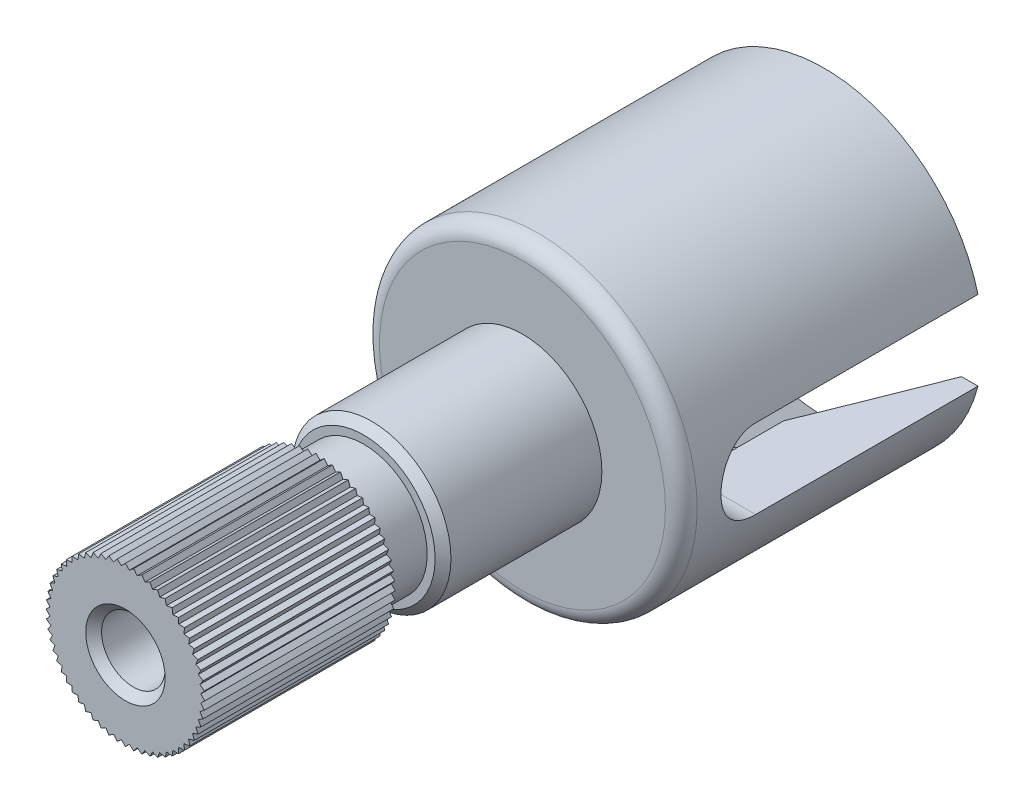
SolidWorks part; units mm, degrees
ref_plane "Plane1" through (0, 0, 0) normal (0, 0, 1) x (1, 0, 0)
ref_plane "Plane2" through (0, 0, 0) normal (0, 1, 0) x (1, 0, 0)
ref_plane "Plane3" through (0, 0, 0) normal (1, 0, 0) x (0, 0, -1)
sketch "Esquisse1" plane through (0, 0, 0) normal (0, 0, 1) x (1, 0, 0)
  circle A0 centre (0, 0) radius 5
  dimension "D1" = 10
extrude "Base-Extrusion" add sketch "Esquisse1" along normal blind 9.5
sketch "Esquisse2" plane through (0, 0, 9.5) normal (0, 0, 1) x (1, 0, 0)
  circle A0 centre (0, 0) radius 2.5
  dimension "D1" = 5
extrude "Boss.-Extru.1" add sketch "Esquisse2" along normal blind 5
fillet "Congé1" radius 0.5
sketch "Esquisse7" plane through (0, 0, 0) normal (1, 0, 0) x (0, 0, -1)
  line L0 (0, 0) -> (-11.8343, 0) construction
  line L1 (-9, 0) -> (0, 0) construction
  line L2 (1, 1.25) -> (-7, 1.25)
  line L3 (1, -1.25) -> (-7, -1.25)
  line L4 (-7, 1.25) -> (-7, -1.25) construction
  line L5 (0, -5) -> (0, 5) construction
  line L6 (1, 1.25) -> (1, -1.25)
  arc A0 (-7, 1.25) -> (-7, -1.25) centre (-7, 0) ccw
  dimension "D1" = 7
  dimension "D2" = 2.5
extrude "Enlèv. mat.-Extru.1" cut sketch "Esquisse7" against normal mid plane 32
sketch "Esquisse8" plane through (0, 0, 0) normal (1, 0, 0) x (0, 0, -1)
  line L0 (0, 4.5) -> (-4, 3)
  line L1 (0, 1.25) -> (0, 5) construction
  line L2 (-4, 3) -> (-8, 3)
  line L3 (-8, 3) -> (-9.5, 0)
  line L4 (-9, 0) -> (0, 0) construction
  line L5 (-9.5, 0) -> (0, 0)
  line L6 (0, 0) -> (0, 4.5)
  line L7 (0, 0) -> (-14.7422, 0) construction
  dimension "D1" = 4
  dimension "D2" = 3
  dimension "D3" = 4
  dimension "D4" = 1.5
  dimension "D5" = 4.5
revolve "Enlèvement de matière-Révolution1" cut sketch "Esquisse8" angle 360 about L7
sketch "Esquisse10" plane through (0, 0, 0) normal (0, 0, 1) x (1, 0, 0)
  line L0 (2.3717, -0.1243) -> (2.4863, -0.2613)
  line L1 (2.3717, -0.1243) -> (2.5, 0)
  line L2 (2.3458, -0.3715) -> (2.4454, -0.5198)
  line L3 (2.3717, 0.1243) -> (2.4863, 0.2613)
  line L4 (2.3717, 0.1243) -> (2.5, 0)
  line L5 (2.3458, -0.3715) -> (2.4863, -0.2613)
  line L6 (2.2941, -0.6147) -> (2.3776, -0.7725)
  line L7 (2.2941, -0.6147) -> (2.4454, -0.5198)
  line L8 (2.2173, -0.8511) -> (2.2839, -1.0168)
  line L9 (2.2173, -0.8511) -> (2.3776, -0.7725)
  line L10 (2.1161, -1.0782) -> (2.1651, -1.25)
  line L11 (2.1161, -1.0782) -> (2.2839, -1.0168)
  line L12 (1.9918, -1.2935) -> (2.0225, -1.4695)
  line L13 (1.9918, -1.2935) -> (2.1651, -1.25)
  line L14 (1.8457, -1.4946) -> (1.8579, -1.6728)
  line L15 (1.8457, -1.4946) -> (2.0225, -1.4695)
  line L16 (1.6794, -1.6794) -> (1.6728, -1.8579)
  line L17 (1.6794, -1.6794) -> (1.8579, -1.6728)
  line L18 (1.4946, -1.8457) -> (1.4695, -2.0225)
  line L19 (1.4946, -1.8457) -> (1.6728, -1.8579)
  line L20 (1.2935, -1.9918) -> (1.25, -2.1651)
  line L21 (1.2935, -1.9918) -> (1.4695, -2.0225)
  line L22 (1.0782, -2.1161) -> (1.0168, -2.2839)
  line L23 (1.0782, -2.1161) -> (1.25, -2.1651)
  line L24 (0.8511, -2.2173) -> (0.7725, -2.3776)
  line L25 (0.8511, -2.2173) -> (1.0168, -2.2839)
  line L26 (0.6147, -2.2941) -> (0.5198, -2.4454)
  line L27 (0.6147, -2.2941) -> (0.7725, -2.3776)
  line L28 (0.3715, -2.3458) -> (0.2613, -2.4863)
  line L29 (0.3715, -2.3458) -> (0.5198, -2.4454)
  line L30 (0.1243, -2.3717) -> (0, -2.5)
  line L31 (0.1243, -2.3717) -> (0.2613, -2.4863)
  line L32 (-0.1243, -2.3717) -> (-0.2613, -2.4863)
  line L33 (-0.1243, -2.3717) -> (0, -2.5)
  line L34 (-0.3715, -2.3458) -> (-0.5198, -2.4454)
  line L35 (-0.3715, -2.3458) -> (-0.2613, -2.4863)
  line L36 (-0.6147, -2.2941) -> (-0.7725, -2.3776)
  line L37 (-0.6147, -2.2941) -> (-0.5198, -2.4454)
  line L38 (-0.8511, -2.2173) -> (-1.0168, -2.2839)
  line L39 (-0.8511, -2.2173) -> (-0.7725, -2.3776)
  line L40 (-1.0782, -2.1161) -> (-1.25, -2.1651)
  line L41 (-1.0782, -2.1161) -> (-1.0168, -2.2839)
  line L42 (-1.2935, -1.9918) -> (-1.4695, -2.0225)
  line L43 (-1.2935, -1.9918) -> (-1.25, -2.1651)
  line L44 (-1.4946, -1.8457) -> (-1.6728, -1.8579)
  line L45 (-1.4946, -1.8457) -> (-1.4695, -2.0225)
  line L46 (-1.6794, -1.6794) -> (-1.8579, -1.6728)
  line L47 (-1.6794, -1.6794) -> (-1.6728, -1.8579)
  line L48 (-1.8457, -1.4946) -> (-2.0225, -1.4695)
  line L49 (-1.8457, -1.4946) -> (-1.8579, -1.6728)
  line L50 (-1.9918, -1.2935) -> (-2.1651, -1.25)
  line L51 (-1.9918, -1.2935) -> (-2.0225, -1.4695)
  line L52 (-2.1161, -1.0782) -> (-2.2839, -1.0168)
  line L53 (-2.1161, -1.0782) -> (-2.1651, -1.25)
  line L54 (-2.2173, -0.8511) -> (-2.3776, -0.7725)
  line L55 (-2.2173, -0.8511) -> (-2.2839, -1.0168)
  line L56 (-2.2941, -0.6147) -> (-2.4454, -0.5198)
  line L57 (-2.2941, -0.6147) -> (-2.3776, -0.7725)
  line L58 (-2.3458, -0.3715) -> (-2.4863, -0.2613)
  line L59 (-2.3458, -0.3715) -> (-2.4454, -0.5198)
  line L60 (-2.3717, -0.1243) -> (-2.5, 0)
  line L61 (-2.3717, -0.1243) -> (-2.4863, -0.2613)
  line L62 (-2.3717, 0.1243) -> (-2.4863, 0.2613)
  line L63 (-2.3717, 0.1243) -> (-2.5, 0)
  line L64 (-2.3458, 0.3715) -> (-2.4454, 0.5198)
  line L65 (-2.3458, 0.3715) -> (-2.4863, 0.2613)
  line L66 (-2.2941, 0.6147) -> (-2.3776, 0.7725)
  line L67 (-2.2941, 0.6147) -> (-2.4454, 0.5198)
  line L68 (-2.2173, 0.8511) -> (-2.2839, 1.0168)
  line L69 (-2.2173, 0.8511) -> (-2.3776, 0.7725)
  line L70 (-2.1161, 1.0782) -> (-2.1651, 1.25)
  line L71 (-2.1161, 1.0782) -> (-2.2839, 1.0168)
  line L72 (-1.9918, 1.2935) -> (-2.0225, 1.4695)
  line L73 (-1.9918, 1.2935) -> (-2.1651, 1.25)
  line L74 (-1.8457, 1.4946) -> (-1.8579, 1.6728)
  line L75 (-1.8457, 1.4946) -> (-2.0225, 1.4695)
  line L76 (-1.6794, 1.6794) -> (-1.6728, 1.8579)
  line L77 (-1.6794, 1.6794) -> (-1.8579, 1.6728)
  line L78 (-1.4946, 1.8457) -> (-1.4695, 2.0225)
  line L79 (-1.4946, 1.8457) -> (-1.6728, 1.8579)
  line L80 (-1.2935, 1.9918) -> (-1.25, 2.1651)
  line L81 (-1.2935, 1.9918) -> (-1.4695, 2.0225)
  line L82 (-1.0782, 2.1161) -> (-1.0168, 2.2839)
  line L83 (-1.0782, 2.1161) -> (-1.25, 2.1651)
  line L84 (-0.8511, 2.2173) -> (-0.7725, 2.3776)
  line L85 (-0.8511, 2.2173) -> (-1.0168, 2.2839)
  line L86 (-0.6147, 2.2941) -> (-0.5198, 2.4454)
  line L87 (-0.6147, 2.2941) -> (-0.7725, 2.3776)
  line L88 (-0.3715, 2.3458) -> (-0.2613, 2.4863)
  line L89 (-0.3715, 2.3458) -> (-0.5198, 2.4454)
  line L90 (-0.1243, 2.3717) -> (0, 2.5)
  line L91 (-0.1243, 2.3717) -> (-0.2613, 2.4863)
  line L92 (0.1243, 2.3717) -> (0.2613, 2.4863)
  line L93 (0.1243, 2.3717) -> (0, 2.5)
  line L94 (0.3715, 2.3458) -> (0.5198, 2.4454)
  line L95 (0.3715, 2.3458) -> (0.2613, 2.4863)
  line L96 (0.6147, 2.2941) -> (0.7725, 2.3776)
  line L97 (0.6147, 2.2941) -> (0.5198, 2.4454)
  line L98 (0.8511, 2.2173) -> (1.0168, 2.2839)
  line L99 (0.8511, 2.2173) -> (0.7725, 2.3776)
  line L100 (1.0782, 2.1161) -> (1.25, 2.1651)
  line L101 (1.0782, 2.1161) -> (1.0168, 2.2839)
  line L102 (1.2935, 1.9918) -> (1.4695, 2.0225)
  line L103 (1.2935, 1.9918) -> (1.25, 2.1651)
  line L104 (1.4946, 1.8457) -> (1.6728, 1.8579)
  line L105 (1.4946, 1.8457) -> (1.4695, 2.0225)
  line L106 (1.6794, 1.6794) -> (1.8579, 1.6728)
  line L107 (1.6794, 1.6794) -> (1.6728, 1.8579)
  line L108 (1.8457, 1.4946) -> (2.0225, 1.4695)
  line L109 (1.8457, 1.4946) -> (1.8579, 1.6728)
  line L110 (1.9918, 1.2935) -> (2.1651, 1.25)
  line L111 (1.9918, 1.2935) -> (2.0225, 1.4695)
  line L112 (2.1161, 1.0782) -> (2.2839, 1.0168)
  line L113 (2.1161, 1.0782) -> (2.1651, 1.25)
  line L114 (2.2173, 0.8511) -> (2.3776, 0.7725)
  line L115 (2.2173, 0.8511) -> (2.2839, 1.0168)
  line L116 (2.2941, 0.6147) -> (2.4454, 0.5198)
  line L117 (2.2941, 0.6147) -> (2.3776, 0.7725)
  line L118 (2.3458, 0.3715) -> (2.4863, 0.2613)
  line L119 (2.3458, 0.3715) -> (2.4454, 0.5198)
sketch "Esquisse11" plane through (0, 0, 14.5) normal (0, 0, 1) x (1, 0, 0)
  circle A0 centre (0, 0) radius 2
  dimension "D1" = 4
extrude "Boss.-Extru.2" add sketch "Esquisse11" along normal blind 1.5
sketch "Esquisse12" plane through (0, 0, 16) normal (0, 0, 1) x (1, 0, 0)
  line L0 (-0.1243, 2.3717) -> (0, 2.5)
  line L1 (0, 2.5) -> (0.1243, 2.3717)
  line L2 (0.2613, 2.4863) -> (0.3715, 2.3458)
  line L3 (0.1243, 2.3717) -> (0.2613, 2.4863)
  line L4 (0.5198, 2.4454) -> (0.6147, 2.2941)
  line L5 (0.3715, 2.3458) -> (0.5198, 2.4454)
  line L6 (0.7725, 2.3776) -> (0.8511, 2.2173)
  line L7 (0.6147, 2.2941) -> (0.7725, 2.3776)
  line L8 (1.0168, 2.2839) -> (1.0782, 2.1161)
  line L9 (0.8511, 2.2173) -> (1.0168, 2.2839)
  line L10 (1.25, 2.1651) -> (1.2935, 1.9918)
  line L11 (1.0782, 2.1161) -> (1.25, 2.1651)
  line L12 (1.4695, 2.0225) -> (1.4946, 1.8457)
  line L13 (1.2935, 1.9918) -> (1.4695, 2.0225)
  line L14 (1.6728, 1.8579) -> (1.6794, 1.6794)
  line L15 (1.4946, 1.8457) -> (1.6728, 1.8579)
  line L16 (1.8579, 1.6728) -> (1.8457, 1.4946)
  line L17 (1.6794, 1.6794) -> (1.8579, 1.6728)
  line L18 (2.0225, 1.4695) -> (1.9918, 1.2935)
  line L19 (1.8457, 1.4946) -> (2.0225, 1.4695)
  line L20 (2.1651, 1.25) -> (2.1161, 1.0782)
  line L21 (1.9918, 1.2935) -> (2.1651, 1.25)
  line L22 (2.2839, 1.0168) -> (2.2173, 0.8511)
  line L23 (2.1161, 1.0782) -> (2.2839, 1.0168)
  line L24 (2.3776, 0.7725) -> (2.2941, 0.6147)
  line L25 (2.2173, 0.8511) -> (2.3776, 0.7725)
  line L26 (2.4454, 0.5198) -> (2.3458, 0.3715)
  line L27 (2.2941, 0.6147) -> (2.4454, 0.5198)
  line L28 (2.4863, 0.2613) -> (2.3717, 0.1243)
  line L29 (2.3458, 0.3715) -> (2.4863, 0.2613)
  line L30 (2.5, 0) -> (2.3717, -0.1243)
  line L31 (2.3717, 0.1243) -> (2.5, 0)
  line L32 (2.4863, -0.2613) -> (2.3458, -0.3715)
  line L33 (2.3717, -0.1243) -> (2.4863, -0.2613)
  line L34 (2.4454, -0.5198) -> (2.2941, -0.6147)
  line L35 (2.3458, -0.3715) -> (2.4454, -0.5198)
  line L36 (2.3776, -0.7725) -> (2.2173, -0.8511)
  line L37 (2.2941, -0.6147) -> (2.3776, -0.7725)
  line L38 (2.2839, -1.0168) -> (2.1161, -1.0782)
  line L39 (2.2173, -0.8511) -> (2.2839, -1.0168)
  line L40 (2.1651, -1.25) -> (1.9918, -1.2935)
  line L41 (2.1161, -1.0782) -> (2.1651, -1.25)
  line L42 (2.0225, -1.4695) -> (1.8457, -1.4946)
  line L43 (1.9918, -1.2935) -> (2.0225, -1.4695)
  line L44 (1.8579, -1.6728) -> (1.6794, -1.6794)
  line L45 (1.8457, -1.4946) -> (1.8579, -1.6728)
  line L46 (1.6728, -1.8579) -> (1.4946, -1.8457)
  line L47 (1.6794, -1.6794) -> (1.6728, -1.8579)
  line L48 (1.4695, -2.0225) -> (1.2935, -1.9918)
  line L49 (1.4946, -1.8457) -> (1.4695, -2.0225)
  line L50 (1.25, -2.1651) -> (1.0782, -2.1161)
  line L51 (1.2935, -1.9918) -> (1.25, -2.1651)
  line L52 (1.0168, -2.2839) -> (0.8511, -2.2173)
  line L53 (1.0782, -2.1161) -> (1.0168, -2.2839)
  line L54 (0.7725, -2.3776) -> (0.6147, -2.2941)
  line L55 (0.8511, -2.2173) -> (0.7725, -2.3776)
  line L56 (0.5198, -2.4454) -> (0.3715, -2.3458)
  line L57 (0.6147, -2.2941) -> (0.5198, -2.4454)
  line L58 (0.2613, -2.4863) -> (0.1243, -2.3717)
  line L59 (0.3715, -2.3458) -> (0.2613, -2.4863)
  line L60 (0, -2.5) -> (-0.1243, -2.3717)
  line L61 (0.1243, -2.3717) -> (0, -2.5)
  line L62 (-0.2613, -2.4863) -> (-0.3715, -2.3458)
  line L63 (-0.1243, -2.3717) -> (-0.2613, -2.4863)
  line L64 (-0.5198, -2.4454) -> (-0.6147, -2.2941)
  line L65 (-0.3715, -2.3458) -> (-0.5198, -2.4454)
  line L66 (-0.7725, -2.3776) -> (-0.8511, -2.2173)
  line L67 (-0.6147, -2.2941) -> (-0.7725, -2.3776)
  line L68 (-1.0168, -2.2839) -> (-1.0782, -2.1161)
  line L69 (-0.8511, -2.2173) -> (-1.0168, -2.2839)
  line L70 (-1.25, -2.1651) -> (-1.2935, -1.9918)
  line L71 (-1.0782, -2.1161) -> (-1.25, -2.1651)
  line L72 (-1.4695, -2.0225) -> (-1.4946, -1.8457)
  line L73 (-1.2935, -1.9918) -> (-1.4695, -2.0225)
  line L74 (-1.6728, -1.8579) -> (-1.6794, -1.6794)
  line L75 (-1.4946, -1.8457) -> (-1.6728, -1.8579)
  line L76 (-1.8579, -1.6728) -> (-1.8457, -1.4946)
  line L77 (-1.6794, -1.6794) -> (-1.8579, -1.6728)
  line L78 (-2.0225, -1.4695) -> (-1.9918, -1.2935)
  line L79 (-1.8457, -1.4946) -> (-2.0225, -1.4695)
  line L80 (-2.1651, -1.25) -> (-2.1161, -1.0782)
  line L81 (-1.9918, -1.2935) -> (-2.1651, -1.25)
  line L82 (-2.2839, -1.0168) -> (-2.2173, -0.8511)
  line L83 (-2.1161, -1.0782) -> (-2.2839, -1.0168)
  line L84 (-2.3776, -0.7725) -> (-2.2941, -0.6147)
  line L85 (-2.2173, -0.8511) -> (-2.3776, -0.7725)
  line L86 (-2.4454, -0.5198) -> (-2.3458, -0.3715)
  line L87 (-2.2941, -0.6147) -> (-2.4454, -0.5198)
  line L88 (-2.4863, -0.2613) -> (-2.3717, -0.1243)
  line L89 (-2.3458, -0.3715) -> (-2.4863, -0.2613)
  line L90 (-2.5, 0) -> (-2.3717, 0.1243)
  line L91 (-2.3717, -0.1243) -> (-2.5, 0)
  line L92 (-2.4863, 0.2613) -> (-2.3458, 0.3715)
  line L93 (-2.3717, 0.1243) -> (-2.4863, 0.2613)
  line L94 (-2.4454, 0.5198) -> (-2.2941, 0.6147)
  line L95 (-2.3458, 0.3715) -> (-2.4454, 0.5198)
  line L96 (-2.3776, 0.7725) -> (-2.2173, 0.8511)
  line L97 (-2.2941, 0.6147) -> (-2.3776, 0.7725)
  line L98 (-2.2839, 1.0168) -> (-2.1161, 1.0782)
  line L99 (-2.2173, 0.8511) -> (-2.2839, 1.0168)
  line L100 (-2.1651, 1.25) -> (-1.9918, 1.2935)
  line L101 (-2.1161, 1.0782) -> (-2.1651, 1.25)
  line L102 (-2.0225, 1.4695) -> (-1.8457, 1.4946)
  line L103 (-1.9918, 1.2935) -> (-2.0225, 1.4695)
  line L104 (-1.8579, 1.6728) -> (-1.6794, 1.6794)
  line L105 (-1.8457, 1.4946) -> (-1.8579, 1.6728)
  line L106 (-1.6728, 1.8579) -> (-1.4946, 1.8457)
  line L107 (-1.6794, 1.6794) -> (-1.6728, 1.8579)
  line L108 (-1.4695, 2.0225) -> (-1.2935, 1.9918)
  line L109 (-1.4946, 1.8457) -> (-1.4695, 2.0225)
  line L110 (-1.25, 2.1651) -> (-1.0782, 2.1161)
  line L111 (-1.2935, 1.9918) -> (-1.25, 2.1651)
  line L112 (-1.0168, 2.2839) -> (-0.8511, 2.2173)
  line L113 (-1.0782, 2.1161) -> (-1.0168, 2.2839)
  line L114 (-0.7725, 2.3776) -> (-0.6147, 2.2941)
  line L115 (-0.8511, 2.2173) -> (-0.7725, 2.3776)
  line L116 (-0.5198, 2.4454) -> (-0.3715, 2.3458)
  line L117 (-0.6147, 2.2941) -> (-0.5198, 2.4454)
  line L118 (-0.2613, 2.4863) -> (-0.1243, 2.3717)
  line L119 (-0.3715, 2.3458) -> (-0.2613, 2.4863)
extrude "Boss.-Extru.3" add sketch "Esquisse12" along normal blind 6
sketch "Esquisse13" plane through (0, 0, 22) normal (0, 0, 1) x (1, 0, 0)
  circle A0 centre (0, 0) radius 1
  dimension "D1" = 2
extrude "Enlèv. mat.-Extru.2" cut sketch "Esquisse13" against normal blind 18
chamfer "Chanfrein1" distance 0.25 angle 45
